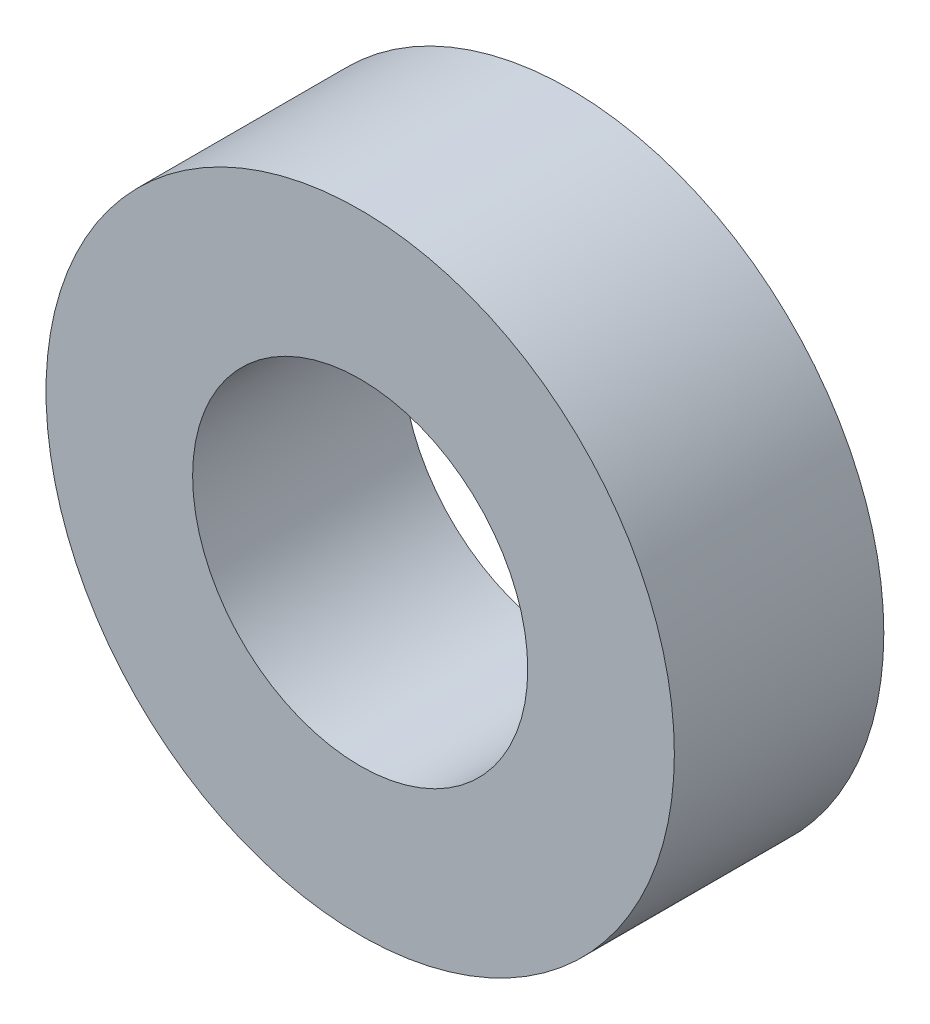
SolidWorks part; units mm, degrees
ref_plane "Front Plane" through (0, 0, 0) normal (0, 0, 1) x (1, 0, 0)
ref_plane "Top Plane" through (0, 0, 0) normal (0, 1, 0) x (1, 0, 0)
ref_plane "Right Plane" through (0, 0, 0) normal (1, 0, 0) x (0, 0, -1)
sketch "Sketch1" plane through (0, 0, 0) normal (0, 0, 1) x (1, 0, 0)
  line L0 (0, 1.6) -> (0, 3) construction
  line L1 (0, -1.6) -> (0, -3) construction
  circle A0 centre (0, 0) radius 3
  circle A1 centre (0, 0) radius 1.6
  dimension "OD" = 6
  dimension "ID" = 3.2
sketch "Sketch2" plane through (0, 0, 0) normal (1, 0, 0) x (0, 0, -1)
  line L0 (-1, 1.6) -> (1, 1.6) construction
  line L1 (-1, -1.6) -> (1, -1.6) construction
  line L2 (-1, -3) -> (1, -3) construction
  line L3 (-1, 3) -> (1, 3) construction
  dimension "Length" = 2
extrude "Extrude1" add sketch "Sketch1" along normal up to vertex (1 mm away) and the other way up to vertex (1 mm away) up to point (0, 1.6, 1) other way up to point (0, 1.6, -1)
sketch "Sketch3" plane through (0, 0, 1) normal (0, 0, 1) x (1, 0, 0)
  circle A0 centre (0, 0) radius 1.6 construction
  circle A3 centre (0, 0) radius 1.6
  point P3 (-1.6, 0)
